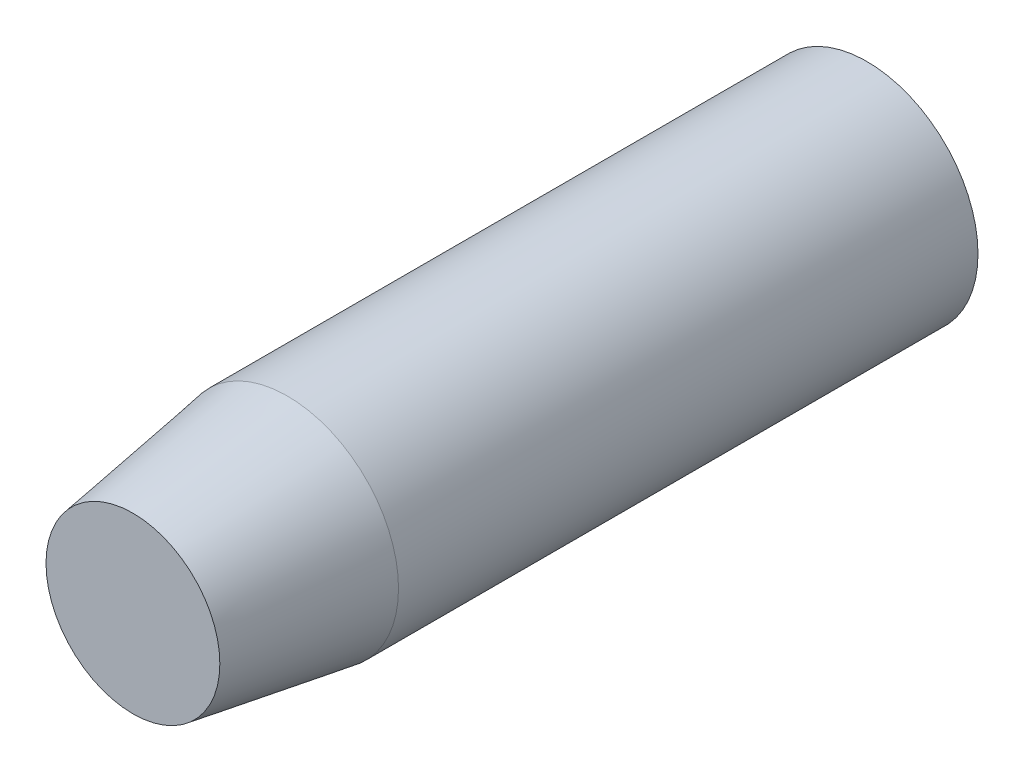
SolidWorks part; units mm, degrees
material "6061-T6 (SS)"
ref_plane "Front Plane" through (0, 0, 0) normal (0, 0, 1) x (1, 0, 0)
ref_plane "Top Plane" through (0, 0, 0) normal (0, 1, 0) x (1, 0, 0)
ref_plane "Right Plane" through (0, 0, 0) normal (1, 0, 0) x (0, 0, -1)
sketch "Sketch1" plane through (0, 0, 0) normal (0, 0, 1) x (1, 0, 0)
  circle A0 centre (0, 0) radius 18.2563
  dimension "D1" = 36.5125
extrude "Boss-Extrude1" add sketch "Sketch1" along normal mid plane 120.65
chamfer "Chamfer1" distance 25.4 distance2 3.9688 1 edges at (18.2563, 0, 60.325)
